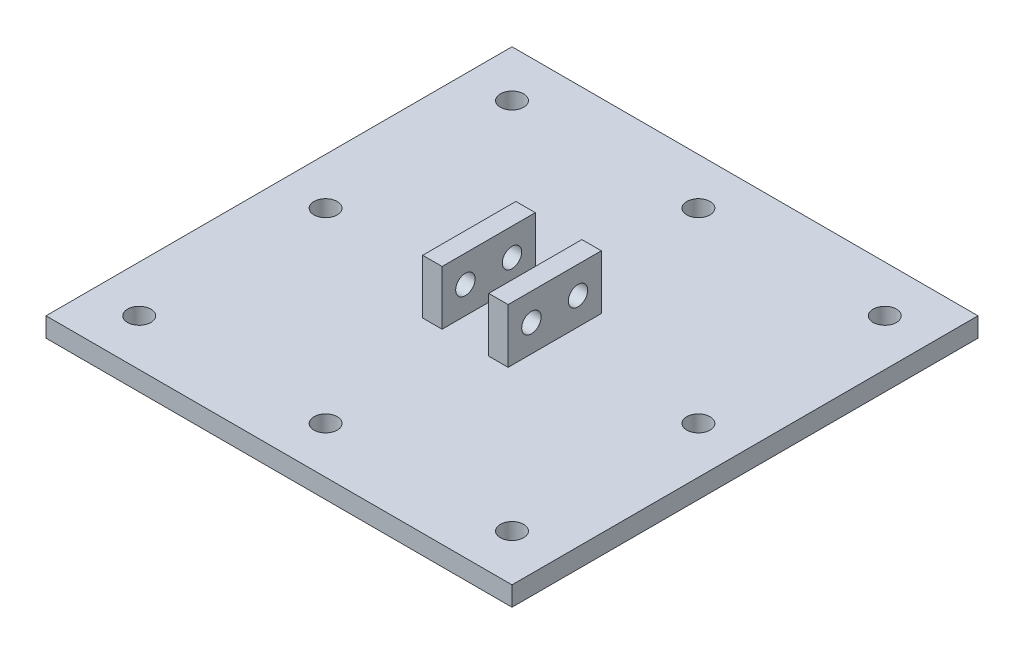
SolidWorks part; units mm, degrees
material "6061-T6 (SS)"
ref_plane "Front Plane" through (0, 0, 0) normal (0, 0, 1) x (1, 0, 0)
ref_plane "Top Plane" through (0, 0, 0) normal (0, 1, 0) x (1, 0, 0)
ref_plane "Right Plane" through (0, 0, 0) normal (1, 0, 0) x (0, 0, -1)
sketch "Sketch2" plane through (0, 0, 0) normal (0, 1, 0) x (1, 0, 0)
  line L1 (-30, -30) -> (30, -30)
  line L2 (-30, -30) -> (-30, 30)
  line L3 (-30, 30) -> (30, 30)
  line L4 (30, -30) -> (30, 30)
  line L5 (-30, -30) -> (30, 30) construction
  line L6 (-30, 30) -> (30, -30) construction
  point P0 (0, 0)
extrude "Boss-Extrude1" add sketch "Sketch2" along normal blind 2.5
sketch "Sketch3" plane through (0, 2.5, 0) normal (0, 1, 0) x (1, 0, 0)
  line L0 (-3, -6) -> (3, -6) construction
  line L1 (-5.5, -6) -> (-3, -6)
  line L2 (-5.5, -6) -> (-5.5, 6)
  line L3 (-5.5, 6) -> (-3, 6)
  line L4 (-3, -6) -> (-3, 6)
  line L5 (-5.5, -6) -> (-3, 6) construction
  line L6 (-5.5, 6) -> (-3, -6) construction
  line L7 (3, -6) -> (5.5, -6)
  line L8 (3, -6) -> (3, 6)
  line L9 (3, 6) -> (5.5, 6)
  line L10 (5.5, -6) -> (5.5, 6)
  line L11 (3, -6) -> (5.5, 6) construction
  line L12 (3, 6) -> (5.5, -6) construction
  line L13 (0, 0) -> (0, -6) construction
  point P0 (-4.25, 0)
  point P5 (4.25, 0)
  dimension "D1" = 6
  dimension "D2" = 2.5
  dimension "D3" = 12
extrude "Boss-Extrude3" add sketch "Sketch3" along normal blind 7
sketch "Sketch6" plane through (-5.5, 0, 0) normal (-1, 0, 0) x (0, 0, 1)
  line L0 (-6, 9.5) -> (-6, 2.5) construction
  line L1 (-6, 6) -> (-3, 6) construction
  line L2 (-3, 6) -> (3, 6) construction
  line L3 (3, 6) -> (6, 6) construction
  line L4 (6, 9.5) -> (6, 2.5) construction
  circle A0 centre (-3, 6) radius 1.25
  circle A1 centre (3, 6) radius 1.25
  dimension "D2" = 2.5
  dimension "D1" = 6
extrude "Cut-Extrude1" cut sketch "Sketch6" against normal up to surface (11 mm away) up to face at (5.5, 6, 0)
sketch "Sketch7" plane through (0, 2.5, 0) normal (0, 1, 0) x (1, 0, 0)
  line L0 (-30, -30) -> (30, -30) construction
  line L1 (24, 24) -> (-24, 24) construction
  line L2 (24, 24) -> (24, -24) construction
  line L3 (24, -24) -> (-24, -24) construction
  line L4 (-24, 24) -> (-24, -24) construction
  line L5 (24, 24) -> (-24, -24) construction
  line L6 (24, -24) -> (-24, 24) construction
  circle A0 centre (24, -24) radius 1.5
  circle A1 centre (-24, -24) radius 1.5
  circle A2 centre (-24, 24) radius 1.5
  circle A3 centre (24, 24) radius 1.5
  circle A4 centre (24, 0) radius 1.5
  circle A5 centre (-24, 0) radius 1.5
  circle A6 centre (0, -24) radius 1.5
  circle A7 centre (0, 24) radius 1.5
  point P8 (0, 0)
  dimension "D1" = 3
  dimension "D2" = 6
extrude "Cut-Extrude2" cut sketch "Sketch7" against normal up to next
